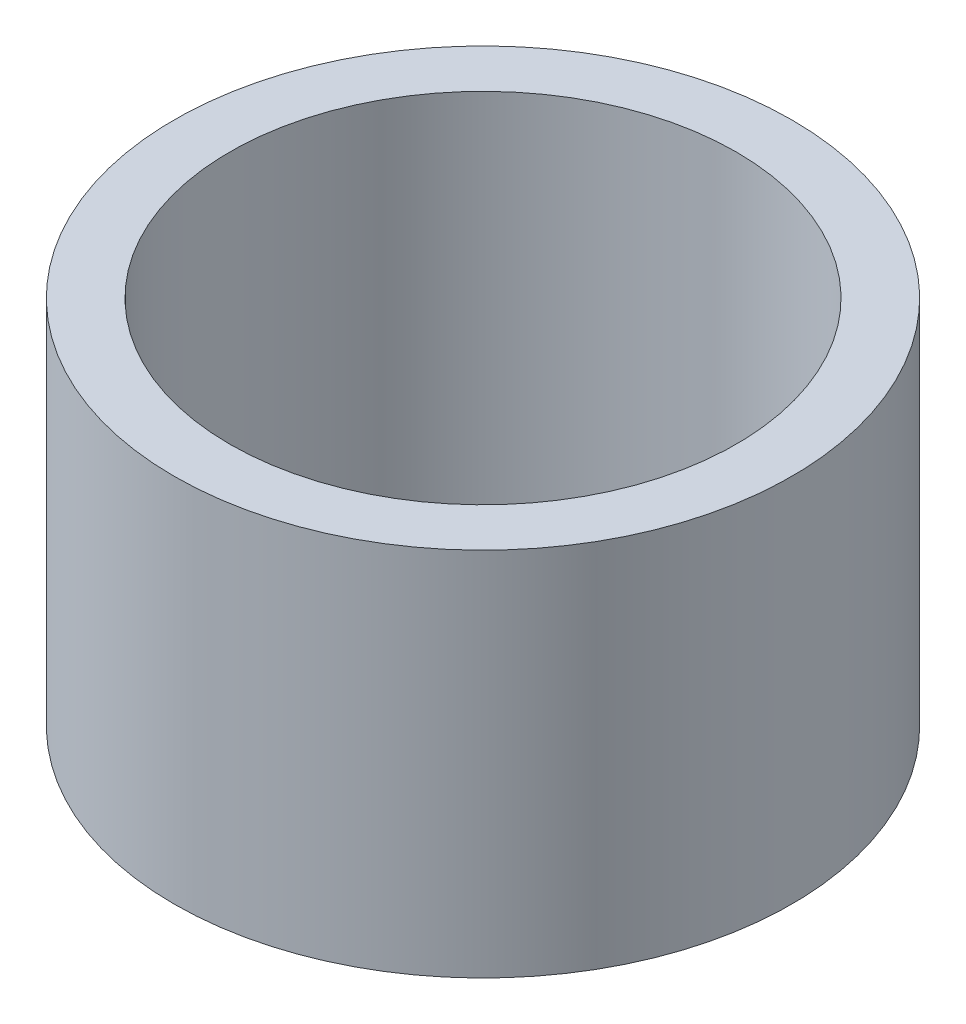
SolidWorks part; units mm, degrees
ref_plane "Alzado" through (0, 0, 0) normal (0, 0, 1) x (1, 0, 0)
ref_plane "Planta" through (0, 0, 0) normal (0, 1, 0) x (1, 0, 0)
ref_plane "Vista lateral" through (0, 0, 0) normal (1, 0, 0) x (0, 0, -1)
sketch "Croquis1" plane through (0, 0, 0) normal (0, 1, 0) x (1, 0, 0)
  circle A0 centre (0, 0) radius 2.5
  dimension "D1" = 5
extrude "Saliente-Extruir1" add sketch "Croquis1" along normal blind 3
sketch "Croquis2" plane through (0, 3, 0) normal (0, 1, 0) x (1, 0, 0)
  circle A0 centre (0, 0) radius 2.05
  dimension "D1" = 4.1
extrude "Cortar-Extruir1" cut sketch "Croquis2" against normal blind 5
